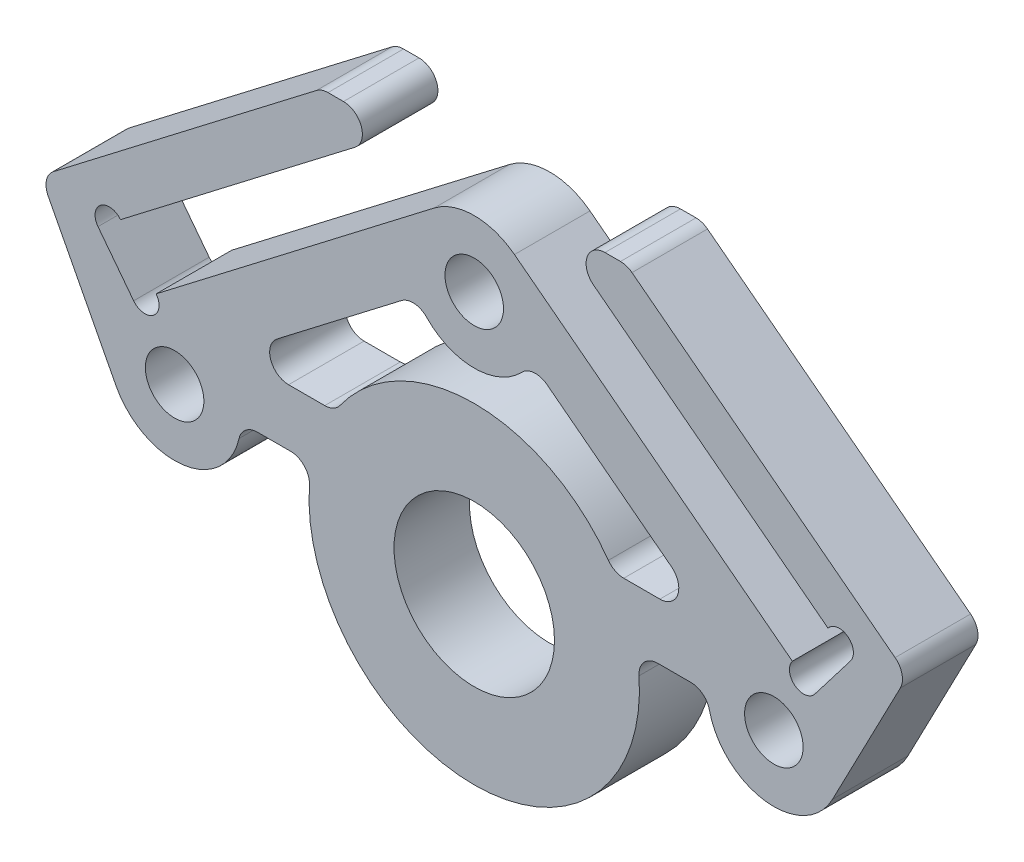
SolidWorks part; units mm, degrees
ref_plane "前视基准面" through (0, 0, 0) normal (0, 0, 1) x (1, 0, 0)
ref_plane "上视基准面" through (0, 0, 0) normal (0, 1, 0) x (1, 0, 0)
ref_plane "右视基准面" through (0, 0, 0) normal (1, 0, 0) x (0, 0, -1)
sketch "草图1" plane through (0, 0, 0) normal (0, 0, 1) x (1, 0, 0)
  line L0 (0, 13.8652) -> (-15.8671, 1.69) construction
  line L1 (0, 13.8652) -> (15.8671, 1.69) construction
  line L2 (-17.9977, 4.4667) -> (-2.1307, 16.6419)
  line L3 (2.1307, 16.6419) -> (17.9977, 4.4667)
  line L4 (-12.3671, 1.69) -> (-8.5852, 1.69)
  line L5 (8.5852, 1.69) -> (12.3671, 1.69)
  circle A0 centre (0, 0) radius 4.25
  circle A1 centre (-15.8671, 1.69) radius 1.55
  circle A2 centre (0, 13.8652) radius 1.55
  circle A3 centre (15.8671, 1.69) radius 1.55
  arc A4 (-8.5852, 1.69) -> (8.5852, 1.69) centre (0, 0) ccw
  arc A5 (-17.9977, 4.4667) -> (-12.3671, 1.69) centre (-15.8671, 1.69) ccw
  arc A6 (2.1307, 16.6419) -> (-2.1307, 16.6419) centre (0, 13.8652) ccw
  arc A7 (12.3671, 1.69) -> (17.9977, 4.4667) centre (15.8671, 1.69) ccw
  dimension "D1" = 105
  dimension "D3" = 8.5
  dimension "D4" = 11
  dimension "D5" = 3.1
  dimension "D6" = 3.5
  dimension "D7" = 4.5
  dimension "D2" = 20
extrude "凸台-拉伸1" add sketch "草图1" along normal mid plane 4
fillet "圆角1" radius 1 4 edges at (12.3671, 1.69, 0) (8.5852, 1.69, 0) (-8.5852, 1.69, 0) (-12.3671, 1.69, 0)
sketch "草图2" plane through (0, 0, 2) normal (0, 0, 1) x (1, 0, 0)
  line L0 (-18.9716, 0.0738) -> (-22.9534, 7.7228)
  line L1 (-2.1307, 16.6419) -> (-17.9977, 4.4667) construction
  line L2 (-22.9534, 7.7228) -> (-8.0849, 19.1318)
  line L3 (-19.9246, 6.8957) -> (-3.9782, 19.1318)
  line L4 (-11.9514, 13.0137) -> (-10.0642, 10.5543) construction
  line L5 (-19.9246, 6.8957) -> (-18.0374, 4.4363)
  line L6 (-8.0849, 19.1318) -> (-3.9782, 19.1318)
  line L7 (-18.0374, 4.4363) -> (-17.9977, 4.4667)
  arc A0 (-17.9977, 4.4667) -> (-12.4546, 0.9122) centre (-15.8671, 1.69) ccw construction
  arc A1 (-17.9977, 4.4667) -> (-18.9716, 0.0738) centre (-15.8671, 1.69) ccw
  dimension "D1" = 80
  dimension "D2" = 3.1
  dimension "D3" = 20.1
  dimension "D4" = 2.5
extrude "凸台-拉伸2" add sketch "草图2" against normal up to surface (4 mm away) up to face at (0, 3.0231, -2)
sketch "草图3" plane through (0, 0, 2) normal (0, 0, 1) x (1, 0, 0)
  line L0 (-19.9246, 6.8957) -> (-3.9782, 19.1318) construction
  line L1 (-2.1307, 16.6419) -> (-18.0374, 4.4363) construction
  circle A0 centre (-19.3295, 7.3522) radius 0.75
  circle A1 centre (-17.4424, 4.8928) radius 0.75
  dimension "D1" = 1.5
extrude "切除-拉伸1" cut sketch "草图3" against normal through all
fillet "圆角2" radius 1 3 edges at (-8.0849, 19.1318, 0) (-3.9782, 19.1318, 0) (-22.9534, 7.7228, 0)
mirror "镜向1" about plane through (0, 0, 0) normal (1, 0, 0) of "凸台-拉伸2", "切除-拉伸1", "圆角2"
sketch "草图4" plane through (0, 0, 2) normal (0, 0, 1) x (1, 0, 0)
  line L0 (-12.7787, 4.69) -> (-3.0526, 12.1531)
  line L1 (-12.7787, 4.69) -> (-7.3869, 4.69)
  line L2 (7.3869, 4.69) -> (12.7787, 4.69)
  line L3 (12.7787, 4.69) -> (3.0526, 12.1531)
  line L4 (9.7256, 1.69) -> (11.4796, 1.69) construction
  line L6 (-2.1307, 16.6419) -> (-16.8474, 5.3494) construction
  line L7 (16.8474, 5.3494) -> (2.1307, 16.6419) construction
  arc A0 (7.3869, 4.69) -> (-7.3869, 4.69) centre (0, 0) ccw
  arc A1 (-3.0526, 12.1531) -> (3.0526, 12.1531) centre (0, 13.8652) ccw
  circle A2 centre (0, 0) radius 4.25 construction
  arc A3 (2.1307, 16.6419) -> (-2.1307, 16.6419) centre (0, 13.8652) ccw construction
  dimension "D1" = 3
  dimension "D3" = 4.5
  dimension "D2" = 3
extrude "切除-拉伸2" cut sketch "草图4" against normal through all
fillet "圆角3" radius 1 6 edges at (-7.3869, 4.69, 0) (7.3869, 4.69, 0) (12.7787, 4.69, 0) (3.0526, 12.1531, 0) (-3.0526, 12.1531, 0) (-12.7787, 4.69, 0)
